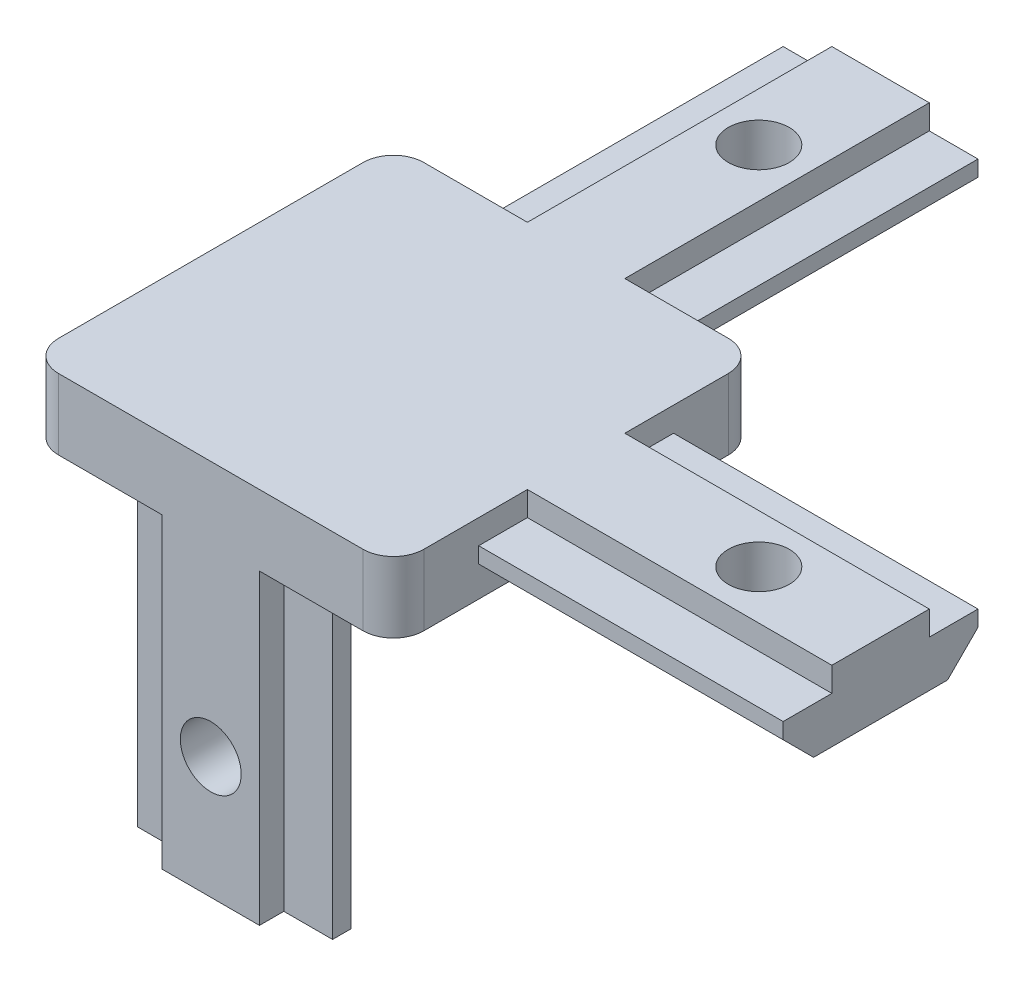
SolidWorks part; units mm, degrees
material "6063-T5"
ref_plane "前视基准面" through (0, 0, 0) normal (0, 0, 1) x (1, 0, 0)
ref_plane "上视基准面" through (0, 0, 0) normal (0, 1, 0) x (1, 0, 0)
ref_plane "右视基准面" through (0, 0, 0) normal (1, 0, 0) x (0, 0, -1)
sketch "草图1" plane through (0, 0, 0) normal (0, 1, 0) x (1, 0, 0)
  line L1 (-15, 15) -> (15, 15)
  line L2 (-15, 15) -> (-15, -15)
  line L3 (-15, -15) -> (15, -15)
  line L4 (15, 15) -> (15, -15)
  line L5 (-15, 15) -> (15, -15) construction
  line L6 (-15, -15) -> (15, 15) construction
  point P0 (0, 0)
  dimension "D1" = 30
  dimension "D2" = 30
extrude "凸台-拉伸1" add sketch "草图1" along normal blind 5.8
sketch "草图2" plane through (0, 0, 0) normal (0, -1, 0) x (-1, 0, 0)
  line L0 (0, 0) -> (0, -15) construction
  line L1 (15, -15) -> (-15, -15) construction
  line L2 (4, -15) -> (4, -13)
  line L3 (4, -13) -> (8, -13)
  line L4 (8, -13) -> (8, -11.5)
  line L5 (5.5, -9) -> (-5.5, -9)
  line L6 (8, -11.5) -> (5.5, -9)
  line L7 (4, -15) -> (-4, -15)
  line L8 (-8, -11.5) -> (-5.5, -9)
  line L9 (-8, -13) -> (-8, -11.5)
  line L10 (-4, -13) -> (-8, -13)
  line L11 (-4, -15) -> (-4, -13)
  line L12 (0, 0) -> (15, -15) construction
  line L13 (15, 4) -> (13, 4)
  line L14 (13, 4) -> (13, 8)
  line L15 (13, 8) -> (11.5, 8)
  line L16 (11.5, 8) -> (9, 5.5)
  line L17 (15, -4) -> (15, 4)
  line L18 (11.5, -8) -> (9, -5.5)
  line L19 (9, -5.5) -> (9, 5.5)
  line L20 (13, -8) -> (11.5, -8)
  line L21 (13, -4) -> (13, -8)
  line L22 (15, -4) -> (13, -4)
  point P7 (8, -9)
  point P14 (0, -9)
  point P17 (-8, -9)
  point P30 (9, 8)
  point P31 (9, 0)
  point P32 (9, -8)
  dimension "D1" = 4
  dimension "D2" = 8
  dimension "D3" = 2
  dimension "D4" = 6
extrude "凸台-拉伸2" add sketch "草图2" along normal blind 25.2
sketch "草图3" plane through (0, 0, 0) normal (0, -1, 0) x (1, 0, 0)
  line L1 (-9, -9) -> (9, -9)
  line L2 (-9, -9) -> (-9, 9)
  line L3 (-9, 9) -> (9, 9)
  line L4 (9, -9) -> (9, 9)
  line L5 (-9, -9) -> (9, 9) construction
  line L6 (-9, 9) -> (9, -9) construction
  point P0 (0, 0)
  dimension "D1" = 18
  dimension "D2" = 18
extrude "切除-拉伸1" cut sketch "草图3" against normal blind 1
sketch "草图5" plane through (0, 0, -15) normal (0, 0, -1) x (-1, 0, 0)
  line L0 (-5.5, 0) -> (5.5, 0)
  line L1 (-15, 0) -> (15, 0) construction
  line L2 (8, 2.5) -> (8, 3.8)
  line L3 (8, 3.8) -> (4, 3.8)
  line L4 (4, 3.8) -> (4, 5.8)
  line L5 (-15, 5.8) -> (15, 5.8) construction
  line L6 (4, 5.8) -> (-4, 5.8)
  line L8 (0, 0) -> (0, 5.8) construction
  line L10 (5.5, 0) -> (8, 2.5)
  line L11 (-5.5, 0) -> (-8, 2.5)
  line L12 (-4, 3.8) -> (-4, 5.8)
  line L13 (-8, 3.8) -> (-4, 3.8)
  line L14 (-8, 2.5) -> (-8, 3.8)
  point P1 (8, 0)
  point P17 (-8, 0)
  dimension "D1" = 2
  dimension "D2" = 4
  dimension "D3" = 8
extrude "凸台-拉伸4" add sketch "草图5" along normal blind 25
sketch "草图7" plane through (0, 0, 0) normal (0, 0, 1) x (1, 0, 0)
  line L0 (0, 0) -> (0, -19.2771) construction
pattern_circular "阵列(圆周)1" count 2 every 90 about axis through (0, 0, 0) along (0, 1, 0) of "凸台-拉伸4"
sketch "草图8" plane through (0, 0, 0) normal (0, -1, 0) x (-1, 0, 0)
  line L0 (-40, -5.5) -> (-40, 5.5) construction
  line L1 (-5.5, 40) -> (5.5, 40) construction
  circle A0 centre (-30, 0) radius 3
  circle A1 centre (0, 30) radius 3
  dimension "D1" = 10
  dimension "D2" = 6
  dimension "D3" = 6
  dimension "D4" = 10
sketch "草图9" plane through (-15, 0, 0) normal (-1, 0, 0) x (0, 0, 1)
  line L0 (4, -25.2) -> (-4, -25.2) construction
  circle A0 centre (0, -15.2) radius 3
  dimension "D1" = 6
  dimension "D2" = 10
sketch "草图10" plane through (0, 0, 15) normal (0, 0, 1) x (1, 0, 0)
  line L0 (4, -25.2) -> (-4, -25.2) construction
  circle A0 centre (0, -15.2) radius 3
  dimension "D1" = 6
  dimension "D2" = 10
hole_wizard "M6 螺纹孔1" positions "草图11" profile "草图12" tap size "M6" standard "GB" end condition through all
sketch "草图11" plane through (0, 0, 0) normal (0, -1, 0) x (-1, 0, 0)
  point P0 (-30, 0)
  point P4 (0, 30)
sketch "草图12" plane through (30, 0, 0) normal (1, 0, 0) x (0, 0, -1)
  line L0 (0, 0) -> (0, 5.8)
  line L1 (0, 5.8) -> (2.5, 5.8)
  line L2 (2.5, 5.8) -> (2.5, 0)
  line L5 (2.5, 0) -> (0, 0)
  line L11 (0, -6.35) -> (0, 107.95) construction
  dimension "通孔螺纹孔钻头直径" = 5
  dimension "通孔螺纹孔钻头深度" = 5.8
cosmetic thread "孔螺蚊线1" parameters "D2"=6
cosmetic thread "孔螺蚊线2" parameters "D2"=6
hole_wizard "M6 螺纹孔2" positions "草图13" profile "草图14" tap size "M6" standard "GB" end condition through all
sketch "草图13" plane through (-15, 0, 0) normal (-1, 0, 0) x (0, 0, 1)
  point P0 (0, -15.2)
sketch "草图14" plane through (-15, -15.2, 0) normal (0, 1, 0) x (0, 0, 1)
  line L0 (0, 0) -> (0, 55)
  line L1 (0, 55) -> (2.5, 55)
  line L2 (2.5, 55) -> (2.5, 0)
  line L5 (2.5, 0) -> (0, 0)
  line L11 (0, -6.35) -> (0, 107.95) construction
  dimension "通孔螺纹孔钻头直径" = 5
  dimension "通孔螺纹孔钻头深度" = 55
cosmetic thread "孔螺蚊线3" parameters "D2"=6
hole_wizard "M6 螺纹孔3" positions "草图15" profile "草图16" tap size "M6" standard "GB" end condition through all
sketch "草图15" plane through (0, 0, 15) normal (0, 0, 1) x (1, 0, 0)
  point P0 (0, -15.2)
sketch "草图16" plane through (0, -15.2, 15) normal (1, 0, 0) x (0, -1, 0)
  line L0 (0, 0) -> (0, 55)
  line L1 (0, 55) -> (2.5, 55)
  line L2 (2.5, 55) -> (2.5, 0)
  line L5 (2.5, 0) -> (0, 0)
  line L11 (0, -6.35) -> (0, 107.95) construction
  dimension "通孔螺纹孔钻头直径" = 5
  dimension "通孔螺纹孔钻头深度" = 55
cosmetic thread "孔螺蚊线4" parameters "D2"=6
fillet "圆角1" radius 2.5 4 edges at (15, 2.9, 15) (15, 2.9, -15) (-15, 2.9, -15) (-15, 2.9, 15)
